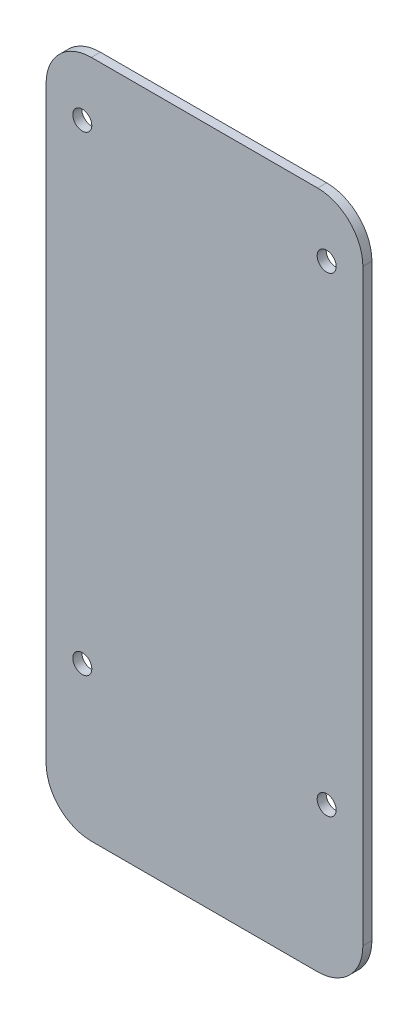
SolidWorks part; units mm, degrees
ref_plane "前视基准面" through (0, 0, 0) normal (0, 0, 1) x (1, 0, 0)
ref_plane "上视基准面" through (0, 0, 0) normal (0, 1, 0) x (1, 0, 0)
ref_plane "右视基准面" through (0, 0, 0) normal (1, 0, 0) x (0, 0, -1)
sketch "草图1" plane through (0, 0, 0) normal (0, 0, 1) x (1, 0, 0)
  line L0 (35, -42) -> (0, -42) construction
  line L1 (-35, 75) -> (35, 75)
  line L2 (-35, 75) -> (-35, -75)
  line L3 (-35, -75) -> (35, -75)
  line L4 (35, 75) -> (35, -75)
  line L5 (0, -75) -> (0, 75) construction
  line L6 (-35, 0) -> (35, 0) construction
  circle A0 centre (-27, 62) radius 2.1
  circle A1 centre (27, 62) radius 2.1
  circle A4 centre (27, -42) radius 2.1
  circle A5 centre (-27, -42) radius 2.1
  point P0 (0, 0)
  dimension "D3" = 4.2
  dimension "D5" = 8
  dimension "D6" = 4.2
  dimension "D8" = 8
  dimension "D1" = 70
  dimension "D2" = 150
  dimension "D4" = 13
  dimension "D7" = 33
extrude "凸台-拉伸1" add sketch "草图1" along normal blind 2
fillet "圆角1" radius 10 4 edges at (35, -75, 1) (-35, -75, 1) (-35, 75, 1) (35, 75, 1)
